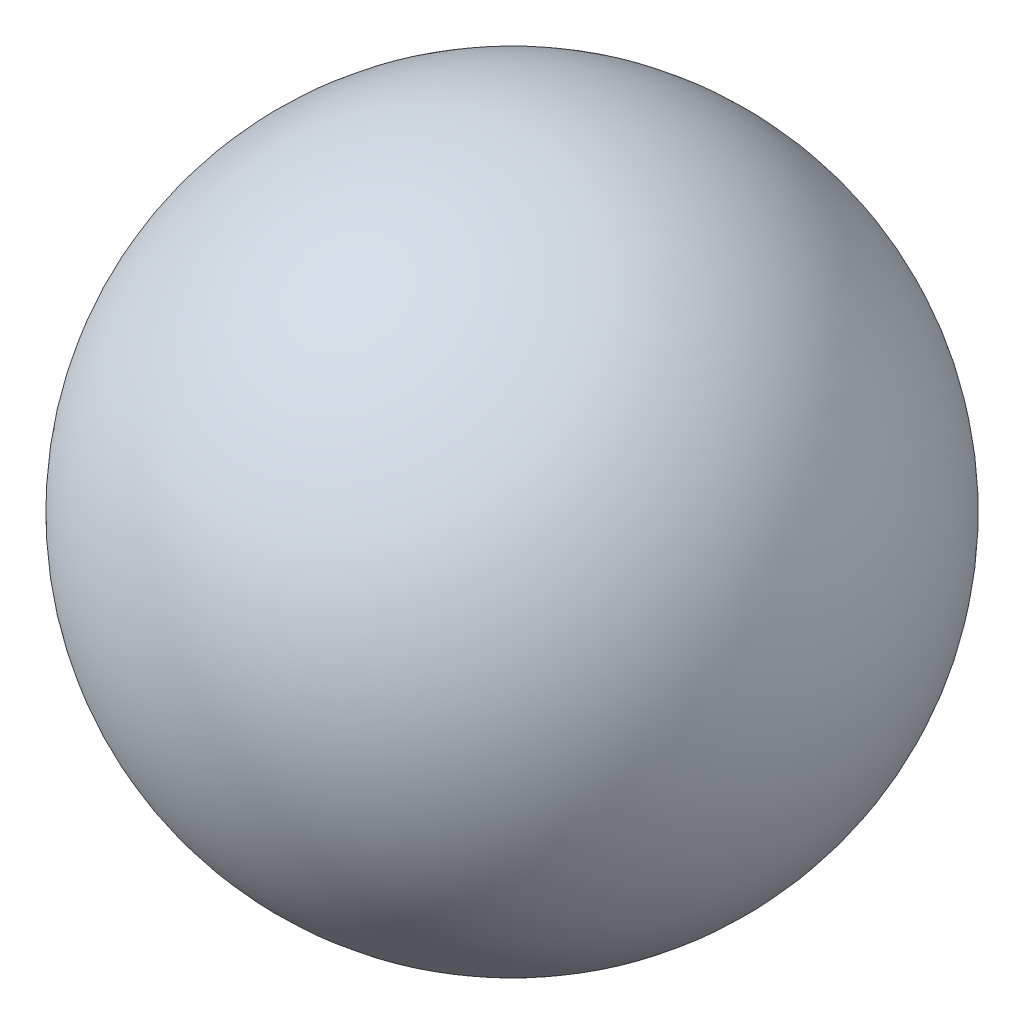
SolidWorks part; units mm, degrees
ref_plane "Piano frontale" through (0, 0, 0) normal (0, 0, 1) x (1, 0, 0)
ref_plane "Piano superiore" through (0, 0, 0) normal (0, 1, 0) x (1, 0, 0)
ref_plane "Piano destro" through (0, 0, 0) normal (1, 0, 0) x (0, 0, -1)
sketch "Schizzo1" plane through (0, 0, 0) normal (1, 0, 0) x (0, 0, -1)
  line L0 (0, -18) -> (0, 18)
  arc A0 (0, 18) -> (0, -18) centre (0, 0) cw
  dimension "D1" = 18
revolve "Rivoluzione1" add sketch "Schizzo1" angle 360 about L0
